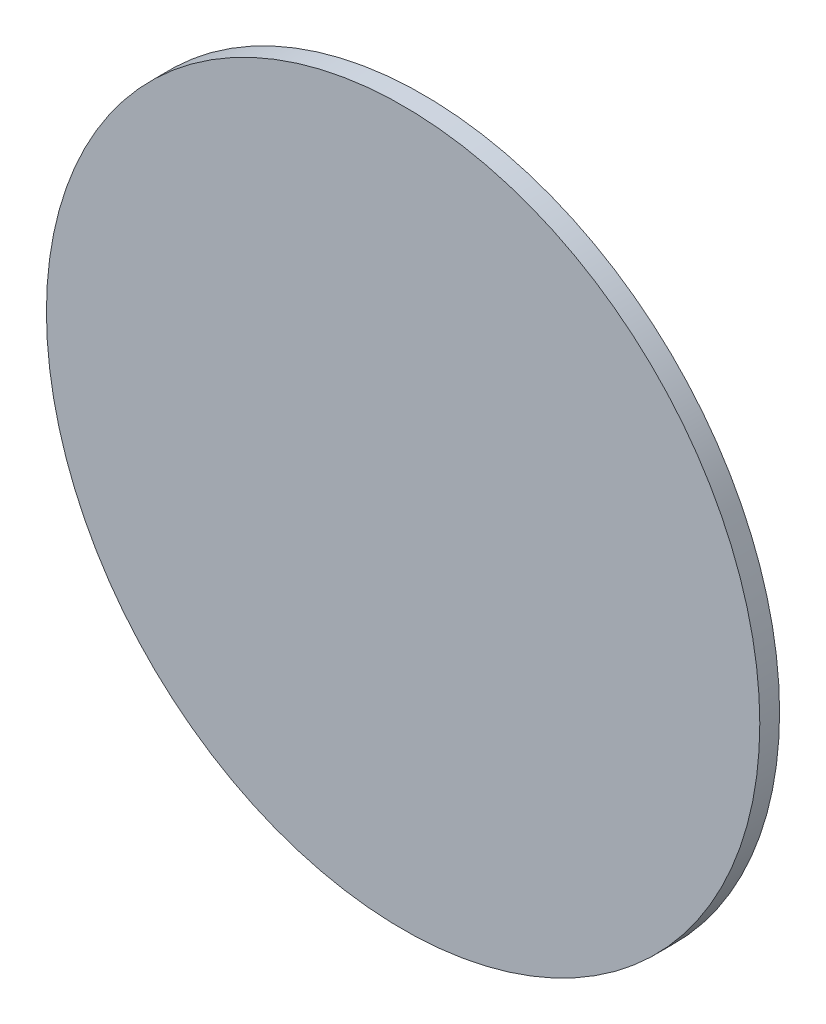
SolidWorks part; units mm, degrees
material "Bismuth"
ref_plane "Front" through (0, 0, 0) normal (0, 0, 1) x (1, 0, 0)
ref_plane "Top" through (0, 0, 0) normal (0, 1, 0) x (1, 0, 0)
ref_plane "Right" through (0, 0, 0) normal (1, 0, 0) x (0, 0, -1)
sketch "Sketch1" plane through (0, 0, 0) normal (0, 0, 1) x (1, 0, 0)
  circle A0 centre (0, 0) radius 133.5
extrude "Boss-Extrude1" add sketch "Sketch1" along normal blind 7.4
